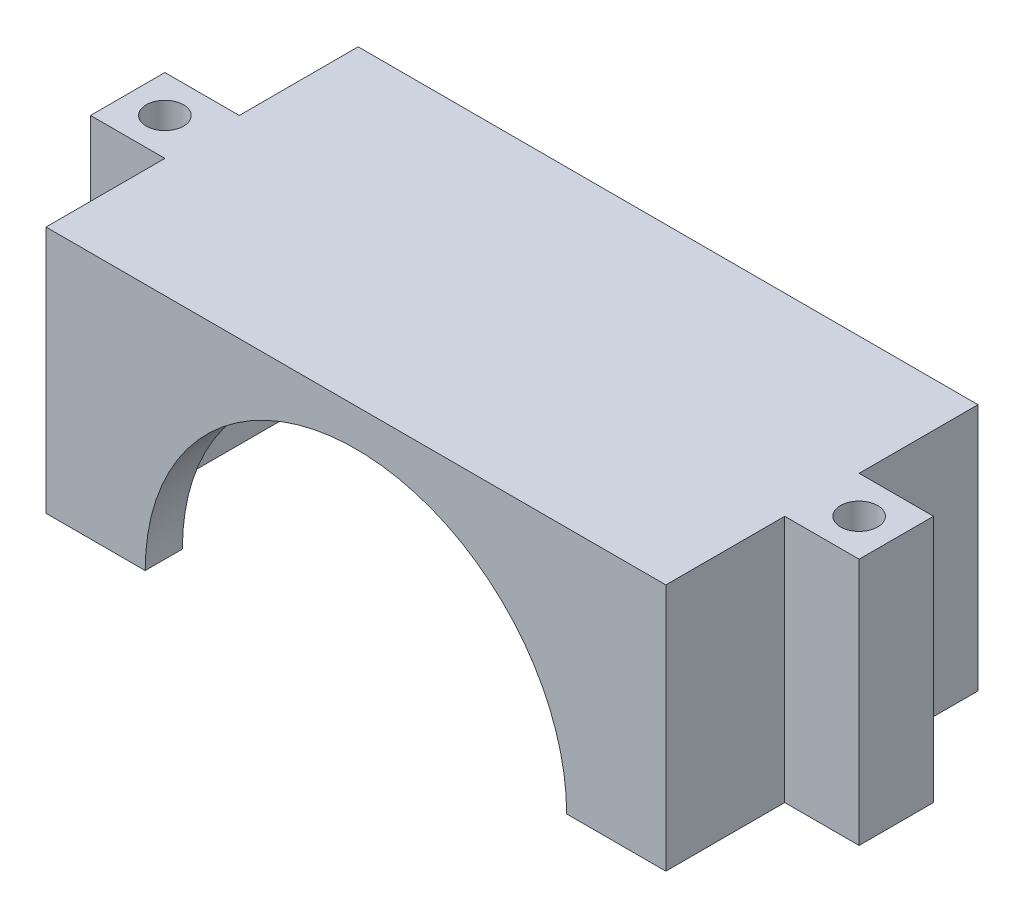
SolidWorks part; units mm, degrees
ref_plane "Front" through (0, 0, 0) normal (0, 0, 1) x (1, 0, 0)
ref_plane "Top" through (0, 0, 0) normal (0, 1, 0) x (1, 0, 0)
ref_plane "Right" through (0, 0, 0) normal (1, 0, 0) x (0, 0, -1)
sketch "Sketch1" plane through (0, 0, 0) normal (0, 1, 0) x (1, 0, 0)
  line L1 (-22, -9.59) -> (22, -9.59) construction
  line L2 (-22, -9.59) -> (-22, 9.59) construction
  line L3 (-22, 9.59) -> (22, 9.59) construction
  line L4 (22, -9.59) -> (22, 9.59) construction
  line L7 (-25, -12.59) -> (25, -12.59)
  line L8 (-25, -12.59) -> (-25, 12.59)
  line L9 (-25, 12.59) -> (25, 12.59)
  line L10 (25, -12.59) -> (25, 12.59)
  line L11 (-25, -12.59) -> (25, 12.59) construction
  line L12 (-25, 12.59) -> (25, -12.59) construction
  point P1 (0, 0)
  point P6 (0, 0)
  dimension "D1" = 44
  dimension "D2" = 19.18
  dimension "D3" = 50
  dimension "D4" = 25.18
extrude "Boss-Extrude1" add sketch "Sketch1" along normal blind 20
sketch "Sketch6" plane through (0, 0, 0) normal (0, -1, 0) x (1, 0, 0)
  line L1 (-22, -9.59) -> (22, -9.59)
  line L2 (-22, -9.59) -> (-22, 9.59)
  line L3 (-22, 9.59) -> (22, 9.59)
  line L4 (22, -9.59) -> (22, 9.59)
  line L5 (-22, -9.59) -> (22, 9.59) construction
  line L6 (-22, 9.59) -> (22, -9.59) construction
  point P0 (0, 0)
  dimension "D1" = 44
  dimension "D2" = 19.18
extrude "Cut-Extrude4" cut sketch "Sketch6" against normal blind 17
sketch "Sketch7" plane through (0, 0, 12.59) normal (0, 0, 1) x (1, 0, 0)
  line L0 (-25, 0) -> (25, 0) construction
  line L1 (-17, 0) -> (17, 0) construction
  line L2 (-17, 0) -> (17, 0)
  arc A0 (17, 0) -> (-17, 0) centre (0, 0) ccw
  point P0 (0, 0)
extrude "Cut-Extrude5" cut sketch "Sketch7" against normal up to surface (3 mm away) up to face at (0, 8.5, 9.59)
sketch "Sketch8" plane through (0, 0, -12.59) normal (0, 0, -1) x (-1, 0, 0)
  line L0 (-25, 20) -> (-25, 0) construction
  line L1 (-22, 0) -> (22, 0) construction
  line L2 (-22, 0) -> (-22, 17) construction
  line L3 (-22, 17) -> (22, 17) construction
  line L4 (22, 0) -> (22, 17) construction
  line L5 (-25, 0) -> (25, 0) construction
  line L6 (-22, 6) -> (-12, 6)
  line L7 (-12, 6) -> (-12, 0)
  line L8 (-22, 0) -> (-12, 0)
  line L9 (-22, 6) -> (-22, 0)
  line M1 (-25, 0) -> (25, 0)
  dimension "D1" = 3
  dimension "D2" = 0
  dimension "D3" = 44
  dimension "D4" = 17
  dimension "D5" = 10
  dimension "D6" = 6
extrude "Cut-Extrude6" cut sketch "Sketch8" against normal blind 17 contours L7 L6 L2 M1
sketch "Sketch9" plane through (0, 20, 0) normal (0, 1, 0) x (1, 0, 0)
  line L0 (25, -12.59) -> (25, 12.59) construction
  line L1 (0, 0) -> (0, -7.3144) construction
  line L2 (25, -3) -> (31, -3)
  line L3 (25, -3) -> (25, 3)
  line L4 (25, 3) -> (31, 3)
  line L5 (31, -3) -> (31, 3)
  line L6 (-25, -3) -> (-25, 3)
  line L7 (-25, -3) -> (-31, -3)
  line L8 (-31, -3) -> (-31, 3)
  line L9 (-25, 3) -> (-31, 3)
  circle A0 centre (28, 0) radius 1.5
  circle A1 centre (-28, 0) radius 1.5
  point P0 (25, -3)
  point P1 (25, 0)
  point P11 (31, 0)
  point P12 (28, 3)
  dimension "D4" = 3
  dimension "D1" = 3
  dimension "D2" = 6
  dimension "D3" = 6
extrude "Boss-Extrude2" add sketch "Sketch9" against normal blind 20
